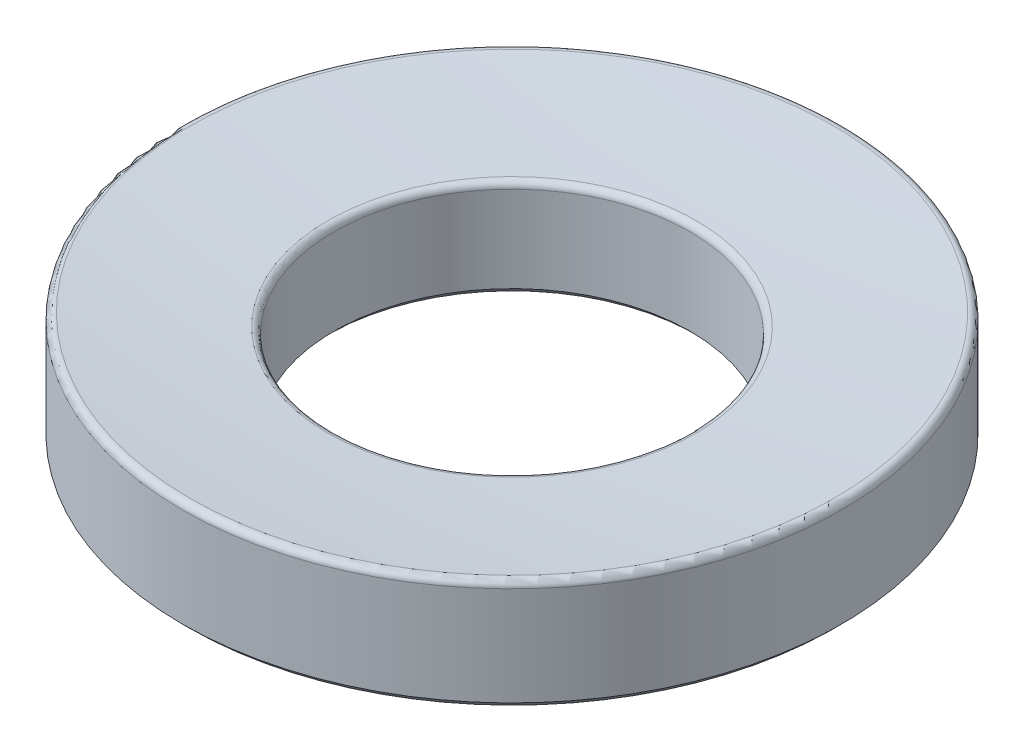
SolidWorks part; units mm, degrees
material "304 SSTL"
ref_plane "Front" through (0, 0, 0) normal (0, 0, 1) x (1, 0, 0)
ref_plane "Top" through (0, 0, 0) normal (0, 1, 0) x (1, 0, 0)
ref_plane "Right" through (0, 0, 0) normal (1, 0, 0) x (0, 0, -1)
sketch "Sketch1" plane through (0, 0, 0) normal (0, 0, 1) x (1, 0, 0)
  line L0 (0, 0) -> (0, -106.68) construction
  line L2 (6.858, -110.2693) -> (12.7, -110.2693)
  line L3 (12.7, -110.2693) -> (12.7, -105.9214)
  line L6 (6.858, -106.4593) -> (6.858, -110.2693)
  arc A0 (6.858, -106.4593) -> (12.7, -105.9214) centre (0, 0) ccw construction
  arc A1 (6.858, -106.4593) -> (12.7, -105.9214) centre (0, 0) ccw
  circle A2 centre (0, 0) radius 106.68 construction
  dimension "D1" = 213.36
  dimension "D2" = 6.858
  dimension "D3" = 12.7
  dimension "D4" = 3.81
revolve "Concave Revolve" add sketch "Sketch1" angle 360 about L0
fillet "Fillet3" radius 0.254 2 edges at (0, -106.4593, 6.858) (0, -105.9214, 12.7)
chamfer "Chamfer2" distance 0.254 angle 45 2 edges at (0, -110.2693, 12.7) (0, -110.2693, 6.858)
